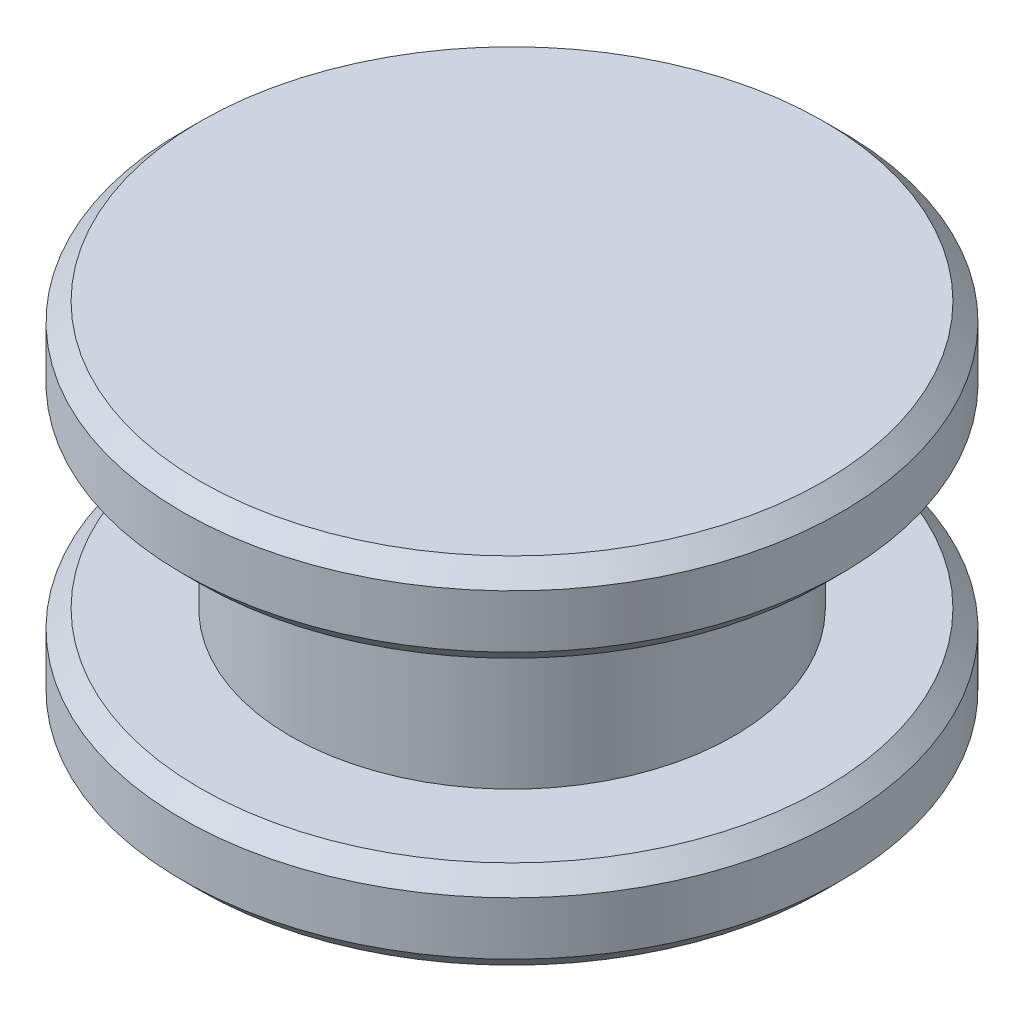
SolidWorks part; units mm, degrees
ref_plane "Front Plane" through (0, 0, 0) normal (0, 0, 1) x (1, 0, 0)
ref_plane "Top Plane" through (0, 0, 0) normal (0, 1, 0) x (1, 0, 0)
ref_plane "Right Plane" through (0, 0, 0) normal (1, 0, 0) x (0, 0, -1)
sketch "Sketch2" plane through (0, 0, 0) normal (0, 1, 0) x (1, 0, 0)
  circle A0 centre (0, 0) radius 0.25
  dimension "D1" = 0.5
extrude "Boss-Extrude1" add sketch "Sketch2" along normal blind 0.2
sketch "Sketch3" plane through (0, 0.2, 0) normal (0, 1, 0) x (1, 0, 0)
  circle A0 centre (0, 0) radius 0.3719
extrude "Boss-Extrude2" add sketch "Sketch3" along normal blind 0.1
sketch "Sketch4" plane through (0, 0, 0) normal (0, -1, 0) x (1, 0, 0)
  circle A0 centre (0, 0) radius 0.3719
extrude "Boss-Extrude3" add sketch "Sketch4" along normal blind 0.1
chamfer "Chamfer1" distance 0.02 angle 45 1 edges at (0, 0.3, 0.3719)
chamfer "Chamfer2" distance 0.02 angle 45 2 edges at (0, 0, -0.3719) (0, 0.2, 0.3719)
chamfer "Chamfer3" distance 0.02 angle 45 1 edges at (0, -0.1, -0.3719)
